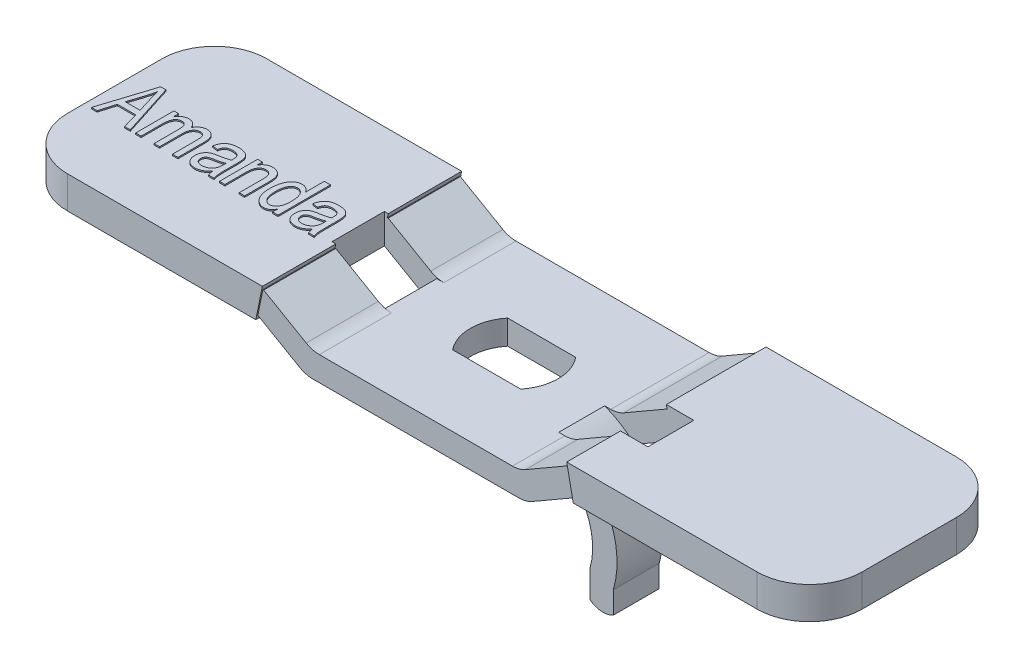
SolidWorks part; units mm, degrees
material "AISI 304"
ref_plane "Front Plane" through (0, 0, 0) normal (0, 0, 1) x (1, 0, 0)
ref_plane "Top Plane" through (0, 0, 0) normal (0, 1, 0) x (1, 0, 0)
ref_plane "Right Plane" through (0, 0, 0) normal (1, 0, 0) x (0, 0, -1)
sketch "Sketch1" plane through (0, 0, 0) normal (0, 0, 1) x (1, 0, 0)
  line L3 (-38.3113, 5.08) -> (-14.7424, 5.08)
  line L8 (-15.3754, 2.7178) -> (-38.3113, 2.7178)
  line L9 (-38.3113, 2.7178) -> (-38.3113, 5.08)
  line L10 (-10.668, 0) -> (-15.3754, 2.7178)
  line L11 (10.668, 0) -> (15.3754, 2.7178)
  line L12 (10.0351, 2.3622) -> (14.7424, 5.08)
  line L13 (-10.668, 0) -> (10.668, 0)
  line L14 (-10.0351, 2.3622) -> (10.0351, 2.3622)
  line L15 (15.3754, 2.7178) -> (37.8887, 2.7178)
  line L16 (-10.0351, 2.3622) -> (-14.7424, 5.08)
  line L17 (14.7424, 5.08) -> (37.8887, 5.08)
  line L18 (-10.0351, 2.3622) -> (10.0351, 2.3622)
  line L19 (37.8887, 2.7178) -> (37.8887, 5.08)
  line L20 (10.668, 0) -> (19.4668, 5.08) construction
  line L25 (-10.668, 0) -> (-19.4668, 5.08) construction
  line L26 (-10.0351, 2.3622) -> (-18.2857, 7.1257) construction
  line L27 (10.0351, 2.3622) -> (18.2857, 7.1257) construction
  point P4 (0, 0)
  point P5 (-35.9491, 2.3622)
  point P7 (35.5265, 2.3622)
  point P8 (35.5265, 2.7178)
  point P9 (-35.9491, 2.7178)
  dimension "D1" = 76.2
  dimension "D2" = 5.08
  dimension "D3" = 2.3622
  dimension "D4" = 2.3622
  dimension "D5" = 22.5134
  dimension "D6" = 21.336
  dimension "D7" = 30
  dimension "D8" = 30
  dimension "D9" = 2.3622
extrude "Boss-Extrude1" add sketch "Sketch1" along normal mid plane 19.05 contours L15 L19 L17 L12 L14 L16 L3 L9 L8 L10 L13 L11
fillet "Fillet1" radius 5.08 4 edges at (37.8887, 3.8989, -9.525) (37.8887, 3.8989, 9.525) (-38.3113, 3.8989, 9.525) (-38.3113, 3.8989, -9.525)
sketch "Sketch3" plane through (0, 0, 0) normal (0, 0, 1) x (1, 0, 0)
  line L4 (-38.3113, 5.461) -> (-33.2313, 5.461)
  line L5 (-33.2313, 5.461) -> (-14.7424, 5.461)
  line L7 (-38.6923, 5.461) -> (-14.7424, 5.461)
  line L10 (15.3754, 2.3368) -> (32.8087, 2.3368)
  line L11 (-33.2313, 2.3368) -> (-38.3113, 2.3368)
  line L12 (-15.3754, 2.3368) -> (-33.2313, 2.3368)
  line L13 (15.3754, 2.3368) -> (38.2697, 2.3368)
  line L14 (-15.3754, 2.3368) -> (-38.6923, 2.3368)
  line L18 (38.2697, 5.461) -> (38.2697, 2.3368)
  line L19 (14.7424, 5.461) -> (32.8087, 5.461)
  line L20 (14.7424, 5.461) -> (38.2697, 5.461)
  line L21 (-38.6923, 5.461) -> (-38.6923, 2.3368)
  line L22 (-38.3113, 2.7178) -> (-38.3113, 5.08) construction
  line L23 (37.8887, 5.08) -> (37.8887, 2.7178) construction
  line L24 (-14.7424, 5.461) -> (-15.3754, 2.3368)
  line L25 (14.7424, 5.461) -> (15.3754, 2.3368)
  dimension "D5" = 0.381
  dimension "D6" = 0.381
  dimension "D1" = 0.381
  dimension "D2" = 0.381
  dimension "D3" = 0.381
  dimension "D4" = 0.381
extrude "Boss-Extrude2" add sketch "Sketch3" along normal mid plane 19.304
sketch "Sketch2" plane through (0, 0, 0) normal (0, 1, 0) x (1, 0, 0)
  line L0 (-10.0351, -9.525) -> (-10.0351, 9.525) construction
  line L1 (-10.0351, 2.54) -> (-15.1151, 2.54)
  line L2 (-10.0351, 2.54) -> (-10.0351, -2.54)
  line L3 (-10.0351, -2.54) -> (-15.1151, -2.54)
  line L4 (-15.1151, 2.54) -> (-15.1151, -2.54)
  line L5 (0, 0) -> (26.5905, 0) construction
  line L6 (10.0351, -9.525) -> (10.0351, 9.525) construction
  line L7 (8.7651, 0) -> (17.4011, 0)
  line L8 (8.7651, 0) -> (8.7651, -4.445)
  line L9 (8.7651, -4.445) -> (17.4011, -4.445)
  line L10 (17.4011, 0) -> (17.4011, -4.445)
  line L12 (3.2985, -2.667) -> (-3.2985, -2.667)
  line L14 (3.2985, 2.667) -> (-3.2985, 2.667)
  line L16 (0, 2.667) -> (0, -2.667) construction
  line L17 (3.302, 0) -> (-3.302, 0) construction
  arc A0 (-3.2985, 2.667) -> (-3.2985, -2.667) centre (0, 0) ccw
  arc A1 (3.2985, -2.667) -> (3.2985, 2.667) centre (0, 0) ccw
  point P6 (-10.0351, 0)
  dimension "D8" = 8.4836
  dimension "D1" = 5.08
  dimension "D2" = 5.08
  dimension "D3" = 8.636
  dimension "D4" = 1.27
  dimension "D5" = 4.445
  dimension "D6" = 5.334
  dimension "D7" = 6.597
extrude "Cut-Extrude1" cut sketch "Sketch2" along normal blind 19.05
fillet "Fillet2" radius 5.08 4 edges at (38.2697, 3.8989, -9.652) (38.2697, 3.8989, 9.652) (-38.6923, 3.8989, -9.652) (-38.6923, 3.8989, 9.652)
sketch "Sketch4" plane through (0, 0, 0) normal (0, 0, 1) x (1, 0, 0)
  line L0 (8.7651, 2.3622) -> (8.7651, 0)
  line L1 (11.7741, -7.576) -> (11.7741, -10.1611)
  line L3 (14.0511, -10.3378) -> (14.0511, -8.2047)
  line L4 (8.7651, 2.3622) -> (8.7651, 0) construction
  arc A0 (8.7651, 2.3622) -> (14.0511, -8.2047) centre (5.7675, -5.7429) cw
  arc A1 (8.7651, 0) -> (11.7741, -7.576) centre (5.4704, -5.6941) cw
  arc A2 (11.7741, -10.1611) -> (14.0511, -10.3378) centre (13.0492, -8.4897) ccw
  dimension "D1" = 2.3622
  dimension "D2" = 6.5786
  dimension "D3" = 12.7
  dimension "D4" = 8.6417
  dimension "D5" = 2.1022
  dimension "D6" = 3.0091
  dimension "D7" = 4.2842
  dimension "D8" = 5.2861
  dimension "D9" = 2.9976
extrude "Boss-Extrude3" add sketch "Sketch4" along normal up to surface (4.445 mm away) up to face at (13.4565, 3.0144, 4.445)
fillet "Fillet3" radius 2.54 7 edges at (10.668, 0, 6.985) (10.668, 0, -4.7625) (-10.668, 0, 6.0325) (-10.0351, 2.3622, -6.0325) (10.0351, 2.3622, 6.985) (10.0351, 2.3622, -4.7625) (-10.0351, 2.3622, 6.0325)
sketch "Sketch5" plane through (0, 5.461, 0) normal (0, 1, 0) x (1, 0, 0)
  line L129 (-37.9052, -3.048) -> (-16.7109, -3.048) construction
  text T0 "Amanda" font "Arial Narrow" height 5.08
  dimension "D1" = 2
extrude "Boss-Extrude4" add sketch "Sketch5" along normal blind 0.127
